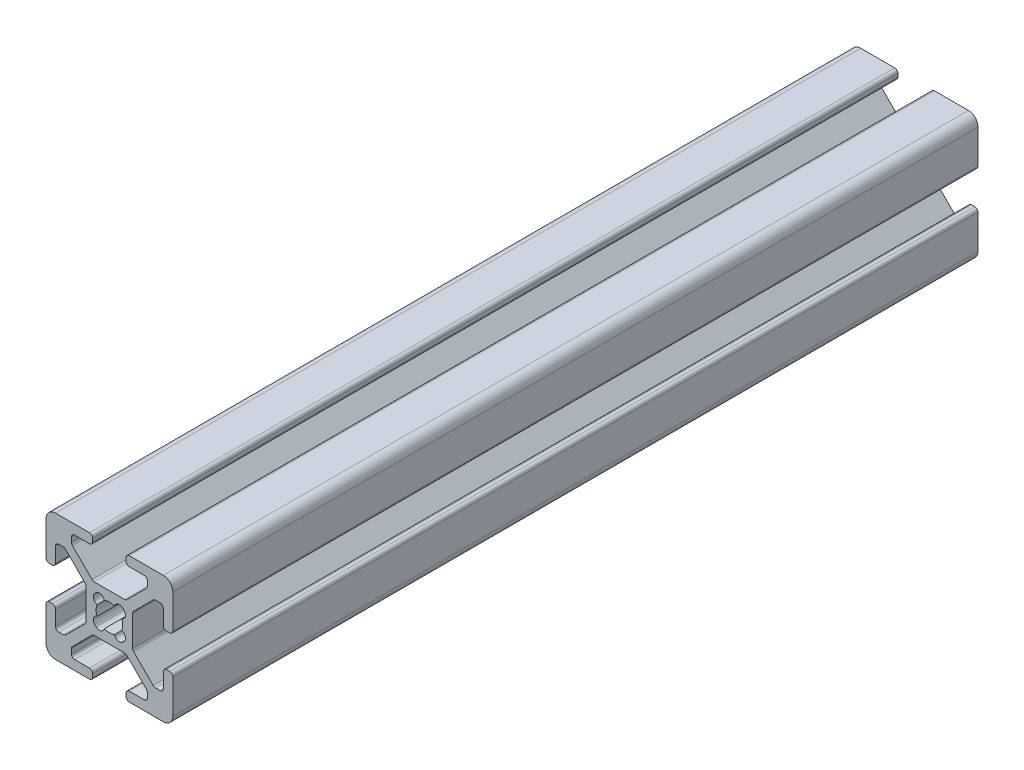
SolidWorks part; units mm, degrees
ref_plane "Front Plane" through (0, 0, 0) normal (0, 0, 1) x (1, 0, 0)
ref_plane "Top Plane" through (0, 0, 0) normal (0, 1, 0) x (1, 0, 0)
ref_plane "Right Plane" through (0, 0, 0) normal (1, 0, 0) x (0, 0, -1)
ref_plane "Plane1" through (0, 0, -4000) normal (0, 0, -1) x (-1, 0, 0)
sketch "Sketch1" plane through (0, 0, -4000) normal (0, 0, -1) x (-1, 0, 0)
  line L0 (2.3045, -2.1245) -> (2.1245, -2.3045)
  line L1 (-2.1245, -2.3045) -> (-2.3045, -2.1245)
  line L2 (-2.3045, 2.1245) -> (-2.1245, 2.3045)
  line L3 (2.1245, 2.3045) -> (2.3045, 2.1245)
  line L4 (10, -8.5) -> (10, -3.138)
  line L5 (9.492, -2.63) -> (9.008, -2.63)
  line L6 (8.5, -3.138) -> (8.5, -5.487)
  line L7 (7.992, -5.995) -> (7.2659, -5.995)
  line L8 (6.9067, -5.8462) -> (3.8038, -2.7433)
  line L9 (3.655, -2.3841) -> (3.655, 2.3838)
  line L10 (3.8038, 2.743) -> (6.907, 5.8462)
  line L11 (7.2662, 5.995) -> (7.992, 5.995)
  line L12 (8.5, 5.487) -> (8.5, 3.138)
  line L13 (9.008, 2.63) -> (9.492, 2.63)
  line L14 (10, 3.138) -> (10, 8.5)
  line L15 (8.5, 10) -> (3.138, 10)
  line L16 (2.63, 9.492) -> (2.63, 9.008)
  line L17 (3.138, 8.5) -> (5.487, 8.5)
  line L18 (5.995, 7.992) -> (5.995, 7.2659)
  line L19 (5.8462, 6.9067) -> (2.7433, 3.8038)
  line L20 (2.3841, 3.655) -> (-2.3838, 3.655)
  line L21 (-2.743, 3.8038) -> (-5.8462, 6.907)
  line L22 (-5.995, 7.2662) -> (-5.995, 7.992)
  line L23 (-5.487, 8.5) -> (-3.138, 8.5)
  line L24 (-2.63, 9.008) -> (-2.63, 9.492)
  line L25 (-3.138, 10) -> (-8.5, 10)
  line L26 (-10, 8.5) -> (-10, 3.138)
  line L27 (-9.492, 2.63) -> (-9.008, 2.63)
  line L28 (-8.5, 3.138) -> (-8.5, 5.487)
  line L29 (-7.992, 5.995) -> (-7.2659, 5.995)
  line L30 (-6.9067, 5.8462) -> (-3.8038, 2.7433)
  line L31 (-3.655, 2.3841) -> (-3.655, -2.3838)
  line L32 (-3.8038, -2.743) -> (-6.907, -5.8462)
  line L33 (-7.2662, -5.995) -> (-7.992, -5.995)
  line L34 (-8.5, -5.487) -> (-8.5, -3.138)
  line L35 (-9.008, -2.63) -> (-9.492, -2.63)
  line L36 (-10, -3.138) -> (-10, -8.5)
  line L37 (-8.5, -10) -> (-3.138, -10)
  line L38 (-2.63, -9.492) -> (-2.63, -9.008)
  line L39 (-3.138, -8.5) -> (-5.487, -8.5)
  line L40 (-5.995, -7.992) -> (-5.995, -7.2659)
  line L41 (-5.8462, -6.9067) -> (-2.7433, -3.8038)
  line L42 (-2.3841, -3.655) -> (2.3838, -3.655)
  line L43 (2.743, -3.8038) -> (5.8462, -6.907)
  line L44 (5.995, -7.2662) -> (5.995, -7.992)
  line L45 (5.487, -8.5) -> (3.138, -8.5)
  line L46 (2.63, -9.008) -> (2.63, -9.492)
  line L47 (3.138, -10) -> (8.5, -10)
  arc A0 (1.9358, 0.8037) -> (1.9358, -0.8037) centre (0, 0) cw
  arc A1 (1.9358, -0.8037) -> (2.3045, -2.1245) centre (1.748, -1.568) cw
  arc A2 (2.1245, -2.3045) -> (0.8037, -1.9358) centre (1.568, -1.748) cw
  arc A3 (0.8037, -1.9358) -> (-0.8037, -1.9358) centre (0, 0) cw
  arc A4 (-0.8037, -1.9358) -> (-2.1245, -2.3045) centre (-1.568, -1.748) cw
  arc A5 (-2.3045, -2.1245) -> (-1.9358, -0.8037) centre (-1.748, -1.568) cw
  arc A6 (-1.9358, -0.8037) -> (-1.9358, 0.8037) centre (0, 0) cw
  arc A7 (-1.9358, 0.8037) -> (-2.3045, 2.1245) centre (-1.748, 1.568) cw
  arc A8 (-2.1245, 2.3045) -> (-0.8037, 1.9358) centre (-1.568, 1.748) cw
  arc A9 (-0.8037, 1.9358) -> (0.8037, 1.9358) centre (0, 0) cw
  arc A10 (0.8037, 1.9358) -> (2.1245, 2.3045) centre (1.568, 1.748) cw
  arc A11 (2.3045, 2.1245) -> (1.9358, 0.8037) centre (1.748, 1.568) cw
  arc A12 (10, -3.138) -> (9.492, -2.63) centre (9.492, -3.138) ccw
  arc A13 (9.008, -2.63) -> (8.5, -3.138) centre (9.008, -3.138) ccw
  arc A14 (8.5, -5.487) -> (7.992, -5.995) centre (7.992, -5.487) cw
  arc A15 (7.2659, -5.995) -> (6.9067, -5.8462) centre (7.2659, -5.487) cw
  arc A16 (3.8038, -2.7433) -> (3.655, -2.3841) centre (4.163, -2.3841) cw
  arc A17 (3.655, 2.3838) -> (3.8038, 2.743) centre (4.163, 2.3838) cw
  arc A18 (6.907, 5.8462) -> (7.2662, 5.995) centre (7.2662, 5.487) cw
  arc A19 (7.992, 5.995) -> (8.5, 5.487) centre (7.992, 5.487) cw
  arc A20 (8.5, 3.138) -> (9.008, 2.63) centre (9.008, 3.138) ccw
  arc A21 (9.492, 2.63) -> (10, 3.138) centre (9.492, 3.138) ccw
  arc A22 (10, 8.5) -> (8.5, 10) centre (8.5, 8.5) ccw
  arc A23 (3.138, 10) -> (2.63, 9.492) centre (3.138, 9.492) ccw
  arc A24 (2.63, 9.008) -> (3.138, 8.5) centre (3.138, 9.008) ccw
  arc A25 (5.487, 8.5) -> (5.995, 7.992) centre (5.487, 7.992) cw
  arc A26 (5.995, 7.2659) -> (5.8462, 6.9067) centre (5.487, 7.2659) cw
  arc A27 (2.7433, 3.8038) -> (2.3841, 3.655) centre (2.3841, 4.163) cw
  arc A28 (-2.3838, 3.655) -> (-2.743, 3.8038) centre (-2.3838, 4.163) cw
  arc A29 (-5.8462, 6.907) -> (-5.995, 7.2662) centre (-5.487, 7.2662) cw
  arc A30 (-5.995, 7.992) -> (-5.487, 8.5) centre (-5.487, 7.992) cw
  arc A31 (-3.138, 8.5) -> (-2.63, 9.008) centre (-3.138, 9.008) ccw
  arc A32 (-2.63, 9.492) -> (-3.138, 10) centre (-3.138, 9.492) ccw
  arc A33 (-8.5, 10) -> (-10, 8.5) centre (-8.5, 8.5) ccw
  arc A34 (-10, 3.138) -> (-9.492, 2.63) centre (-9.492, 3.138) ccw
  arc A35 (-9.008, 2.63) -> (-8.5, 3.138) centre (-9.008, 3.138) ccw
  arc A36 (-8.5, 5.487) -> (-7.992, 5.995) centre (-7.992, 5.487) cw
  arc A37 (-7.2659, 5.995) -> (-6.9067, 5.8462) centre (-7.2659, 5.487) cw
  arc A38 (-3.8038, 2.7433) -> (-3.655, 2.3841) centre (-4.163, 2.3841) cw
  arc A39 (-3.655, -2.3838) -> (-3.8038, -2.743) centre (-4.163, -2.3838) cw
  arc A40 (-6.907, -5.8462) -> (-7.2662, -5.995) centre (-7.2662, -5.487) cw
  arc A41 (-7.992, -5.995) -> (-8.5, -5.487) centre (-7.992, -5.487) cw
  arc A42 (-8.5, -3.138) -> (-9.008, -2.63) centre (-9.008, -3.138) ccw
  arc A43 (-9.492, -2.63) -> (-10, -3.138) centre (-9.492, -3.138) ccw
  arc A44 (-10, -8.5) -> (-8.5, -10) centre (-8.5, -8.5) ccw
  arc A45 (-3.138, -10) -> (-2.63, -9.492) centre (-3.138, -9.492) ccw
  arc A46 (-2.63, -9.008) -> (-3.138, -8.5) centre (-3.138, -9.008) ccw
  arc A47 (-5.487, -8.5) -> (-5.995, -7.992) centre (-5.487, -7.992) cw
  arc A48 (-5.995, -7.2659) -> (-5.8462, -6.9067) centre (-5.487, -7.2659) cw
  arc A49 (-2.7433, -3.8038) -> (-2.3841, -3.655) centre (-2.3841, -4.163) cw
  arc A50 (2.3838, -3.655) -> (2.743, -3.8038) centre (2.3838, -4.163) cw
  arc A51 (5.8462, -6.907) -> (5.995, -7.2662) centre (5.487, -7.2662) cw
  arc A52 (5.995, -7.992) -> (5.487, -8.5) centre (5.487, -7.992) cw
  arc A53 (3.138, -8.5) -> (2.63, -9.008) centre (3.138, -9.008) ccw
  arc A54 (2.63, -9.492) -> (3.138, -10) centre (3.138, -9.492) ccw
  arc A55 (8.5, -10) -> (10, -8.5) centre (8.5, -8.5) ccw
extrude "Boss-Extrude1" add sketch "Sketch1" against normal blind 127
